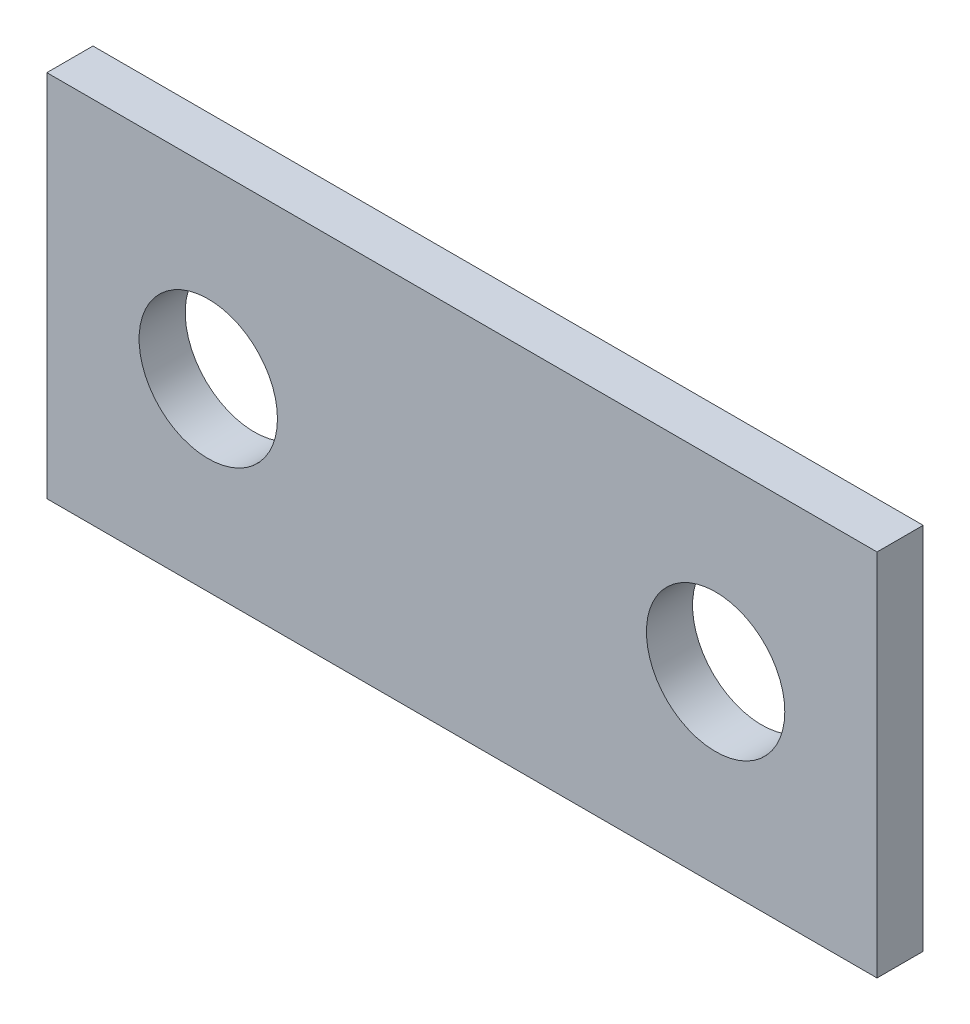
SolidWorks part; units mm, degrees
ref_plane "Front" through (0, 0, 0) normal (0, 0, 1) x (1, 0, 0)
ref_plane "Top" through (0, 0, 0) normal (0, 1, 0) x (1, 0, 0)
ref_plane "Right" through (0, 0, 0) normal (1, 0, 0) x (0, 0, -1)
sketch "Sketch1" plane through (0, 0, 0) normal (0, 0, 1) x (1, 0, 0)
  line L0 (17.4625, 0) -> (-17.4625, 0) construction
  line L1 (28.575, -12.7) -> (-28.575, -12.7)
  line L2 (28.575, -12.7) -> (28.575, 12.7)
  line L3 (28.575, 12.7) -> (-28.575, 12.7)
  line L4 (-28.575, -12.7) -> (-28.575, 12.7)
  line L5 (28.575, -12.7) -> (-28.575, 12.7) construction
  line L6 (28.575, 12.7) -> (-28.575, -12.7) construction
  circle A0 centre (-17.4625, 0) radius 4.7625
  circle A1 centre (17.4625, 0) radius 4.7625
  point P0 (0, 0)
  dimension "Hole Size" = 9.525
  dimension "Length" = 57.15
  dimension "Width" = 25.4
  dimension "Center to Center " = 34.925
extrude "Boss-Extrude1" add sketch "Sketch1" along normal blind 3.175
